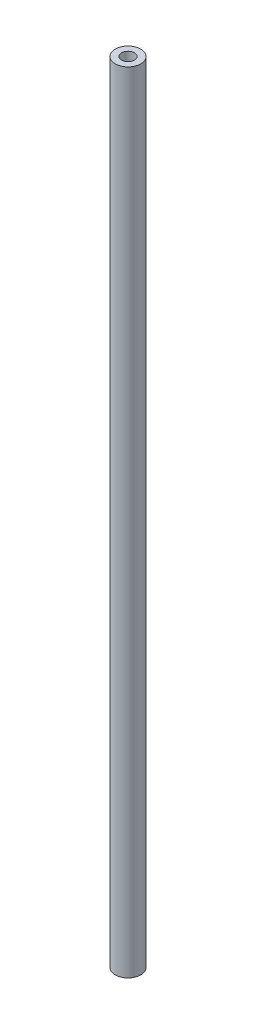
SolidWorks part; units mm, degrees
ref_plane "Front Plane" through (0, 0, 0) normal (0, 0, 1) x (1, 0, 0)
ref_plane "Top Plane" through (0, 0, 0) normal (0, 1, 0) x (1, 0, 0)
ref_plane "Right Plane" through (0, 0, 0) normal (1, 0, 0) x (0, 0, -1)
sketch "Sketch1" plane through (0, 0, 0) normal (0, 1, 0) x (1, 0, 0)
  circle A0 centre (0, 0) radius 6.35
  circle A1 centre (0, 0) radius 3.175
  dimension "D1" = 12.7
  dimension "D2" = 6.35
extrude "Boss-Extrude1" add sketch "Sketch1" along normal blind 391.414
